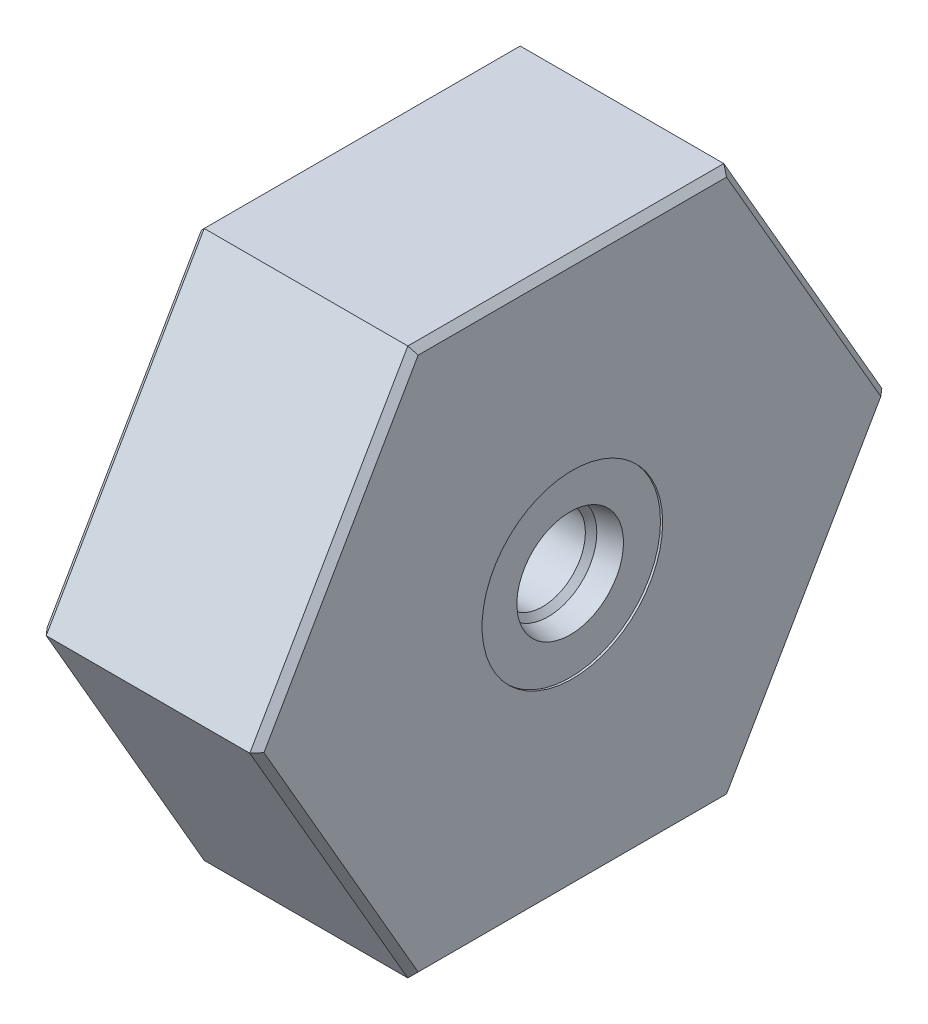
SolidWorks part; units mm, degrees
material "Alloy Steel"
ref_plane "Front Plane" through (0, 0, 0) normal (0, 0, 1) x (1, 0, 0)
ref_plane "Top Plane" through (0, 0, 0) normal (0, 1, 0) x (1, 0, 0)
ref_plane "Right Plane" through (0, 0, 0) normal (1, 0, 0) x (0, 0, -1)
ref_plane "Plane1" through (0, 0, 0) normal (-1, 0, 0) x (0, -1, 0)
sketch "Sketch1" plane through (0, 0, 0) normal (-1, 0, 0) x (0, -1, 0)
  line L0 (31.75, 18.3309) -> (0, 36.6617)
  line L1 (0, 36.6617) -> (-31.75, 18.3309)
  line L2 (-31.75, 18.3309) -> (-31.75, -18.3309)
  line L3 (-31.75, -18.3309) -> (0, -36.6617)
  line L4 (0, -36.6617) -> (31.75, -18.3309)
  line L5 (31.75, -18.3309) -> (31.75, 18.3309)
extrude "Extrude1" add sketch "Sketch1" against normal blind 25.146
sketch "Sketch2" plane through (0, 0, 0) normal (0, 0, 1) x (1, 0, 0)
  line L0 (0, 27.8003) -> (0, 0)
  line L1 (0, 0) -> (25.146, 0)
  line L2 (25.146, 0) -> (25.146, 10.4775)
  line L3 (25.146, 10.4775) -> (24.892, 10.4775)
  line L4 (24.892, 10.4775) -> (24.892, 6.1849)
  line L5 (24.892, 6.1849) -> (22.3393, 5.6423)
  line L6 (22.3393, 5.6423) -> (21.6754, 4.9784)
  line L7 (21.6754, 4.9784) -> (14.986, 4.9784)
  line L8 (14.986, 4.9784) -> (14.986, 27.4955)
  line L9 (14.986, 27.4955) -> (12.7, 27.4955)
  line L10 (12.2344, 27.8003) -> (0, 27.8003)
  line L11 (0, 0) -> (25.146, 0) construction
  arc A0 (12.7, 27.4955) -> (12.2344, 27.8003) centre (12.2344, 27.2923) ccw
revolve "Cut-Revolve1" cut sketch "Sketch2" angle 360 about L11
hole_wizard "Hole1" positions "Sketch4" profile "Sketch3" legacy
sketch "Sketch4" plane through (14.986, 0, 0) normal (-1, 0, 0) x (0, 0, 1)
  point P0 (0, 15.24)
sketch "Sketch3" plane through (14.986, 15.24, 0) normal (0, 1, 0) x (0, 0, 1)
  line L0 (0, 0) -> (0, 2.286)
  line L1 (0, 2.286) -> (8.001, 2.286)
  line L2 (8.001, 2.286) -> (8.001, 0)
  line L3 (8.001, 0) -> (0, 0)
  line L4 (0, 110) -> (0, -10) construction
  dimension "Diameter" = 16.002
  dimension "Depth" = 2.286
chamfer "Chamfer1" distance 0.254 angle 45 1 edges at (0, 0, -27.8003)
chamfer "Chamfer2" distance 0.762 angle 45 1 edges at (14.986, 0, -4.9784)
chamfer "Chamfer3" distance 0.762 angle 45 6 edges at (0, 15.875, -27.4963) (0, -15.875, -27.4963) (0, 31.75, 0) (0, -31.75, 0) (0, 15.875, 27.4963) (0, -15.875, 27.4963)
chamfer "Chamfer4" distance 0.762 angle 45 6 edges at (25.146, 15.875, -27.4963) (25.146, 31.75, 0) (25.146, -15.875, -27.4963) (25.146, 15.875, 27.4963) (25.146, -31.75, 0) (25.146, -15.875, 27.4963)
